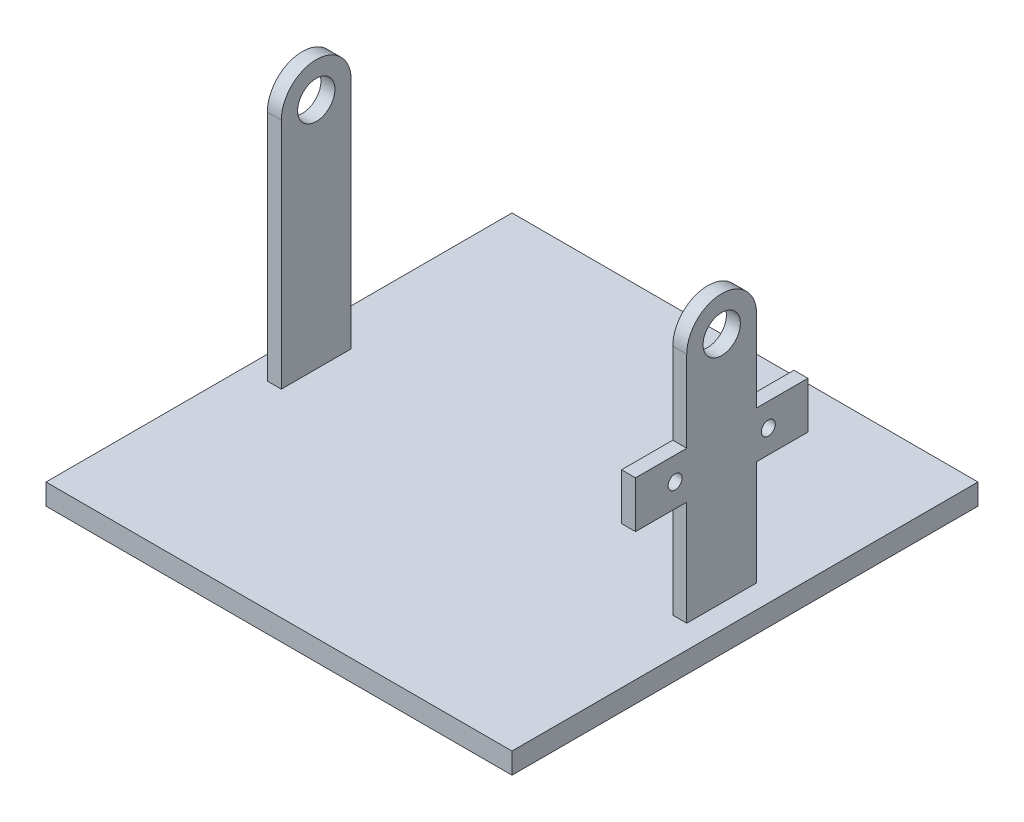
SolidWorks part; units mm, degrees
ref_plane "Front Plane" through (0, 0, 0) normal (0, 0, 1) x (1, 0, 0)
ref_plane "Top Plane" through (0, 0, 0) normal (0, 1, 0) x (1, 0, 0)
ref_plane "Right Plane" through (0, 0, 0) normal (1, 0, 0) x (0, 0, -1)
sketch "Sketch1" plane through (0, 0, 0) normal (0, 1, 0) x (1, 0, 0)
  line L1 (-50, -50) -> (50, -50)
  line L2 (-50, -50) -> (-50, 50)
  line L3 (-50, 50) -> (50, 50)
  line L4 (50, -50) -> (50, 50)
  line L5 (-50, -50) -> (50, 50) construction
  line L6 (-50, 50) -> (50, -50) construction
  point P0 (0, 0)
  dimension "D1" = 100
  dimension "D2" = 100
extrude "Boss-Extrude1" add sketch "Sketch1" along normal blind 4.5
sketch "Sketch2" plane through (0, 4.5, 0) normal (0, 1, 0) x (1, 0, 0)
  line L0 (-50, 0) -> (50, 0) construction
  line L1 (-50, 50) -> (-50, -50) construction
  line L2 (50, -50) -> (50, 50) construction
  line L3 (-45, 0) -> (-45, 13) construction
  line L4 (50, 50) -> (-50, 50) construction
  line L5 (0, 50) -> (0, -50) construction
  line L6 (-50, -50) -> (50, -50) construction
  line L7 (-45, -45) -> (45, -45) construction
  line L8 (-45, -45) -> (-45, 45) construction
  line L9 (-45, 45) -> (45, 45) construction
  line L10 (45, -45) -> (45, 45) construction
  line L11 (-45, -45) -> (45, 45) construction
  line L12 (-45, 45) -> (45, -45) construction
  line L13 (-45, 13) -> (-41, 13) construction
  line L14 (-41, 13) -> (-41, 8) construction
  line L15 (-41, 8) -> (-38, 8) construction
  line L16 (-38, 8) -> (-38, 13) construction
  line L17 (-38, 13) -> (-41, 13) construction
  line L29 (-45, 0) -> (-43.5, 0) construction
  line L30 (45, 7.5) -> (42, 7.5)
  line L31 (-45, -7.5) -> (-42, -7.5)
  line L32 (-45, -7.5) -> (-45, 7.5)
  line L33 (-45, 7.5) -> (-42, 7.5)
  line L34 (-42, -7.5) -> (-42, 7.5)
  line L35 (-45, -7.5) -> (-42, 7.5) construction
  line L36 (-45, 7.5) -> (-42, -7.5) construction
  line L37 (42, -7.5) -> (42, 7.5)
  line L38 (45, -7.5) -> (42, -7.5)
  line L39 (45, -7.5) -> (45, 7.5)
  point P6 (0, 0)
  dimension "D1" = 90
  dimension "D2" = 90
  dimension "D3" = 13
  dimension "D4" = 4
  dimension "D5" = 3
  dimension "D6" = 8
  dimension "D7" = 15
  dimension "D8" = 3
  dimension "D9" = 0
extrude "Boss-Extrude2" add sketch "Sketch2" along normal blind 60
sketch "Sketch3" plane through (45, 0, 0) normal (1, 0, 0) x (0, 0, -1)
  line L0 (0, 64.5) -> (0, 4.5) construction
  line L1 (-7.5, 64.5) -> (7.5, 64.5) construction
  line L2 (-7.5, 4.5) -> (7.5, 4.5) construction
  line L3 (-7.5, 4.5) -> (-7.5, 49.5) construction
  line L4 (-7.5, 64.5) -> (-7.5, 4.5) construction
  line L5 (-7.5, 54.5) -> (-7.5, 64.5)
  line L6 (-7.5, 64.5) -> (7.5, 64.5)
  line L7 (7.5, 64.5) -> (7.5, 54.5)
  circle A0 centre (0, 54.5) radius 4
  arc A1 (7.5, 54.5) -> (-7.5, 54.5) centre (0, 54.5) ccw
  dimension "D2" = 8
  dimension "D1" = 45
  dimension "D3" = 10
extrude "Cut-Extrude1" cut sketch "Sketch3" against normal through all
sketch "Sketch4" plane through (45, 0, 0) normal (1, 0, 0) x (0, 0, -1)
  line L0 (0, 58.5) -> (0, 27.02) construction
  line L1 (0, 27.02) -> (18.5, 27.02)
  line L2 (18.5, 27.02) -> (18.5, 37.02)
  line L3 (18.5, 37.02) -> (-18.5, 37.02)
  line L4 (-18.5, 37.02) -> (-18.5, 27.02)
  line L5 (-18.5, 27.02) -> (0, 27.02)
  line L6 (0, 27.02) -> (0, 32.02) construction
  line L7 (0, 32.02) -> (-10, 32.02) construction
  line L12 (0, 32.02) -> (10, 32.02) construction
  circle A1 centre (-10, 32.02) radius 1.5
  circle A2 centre (10, 32.02) radius 1.5
  circle A3 centre (0, 54.5) radius 4 construction
  dimension "D3" = 10
  dimension "D5" = 3
  dimension "D1" = 31.48
  dimension "D2" = 5
  dimension "D4" = 10
extrude "Boss-Extrude3" add sketch "Sketch4" against normal blind 3
